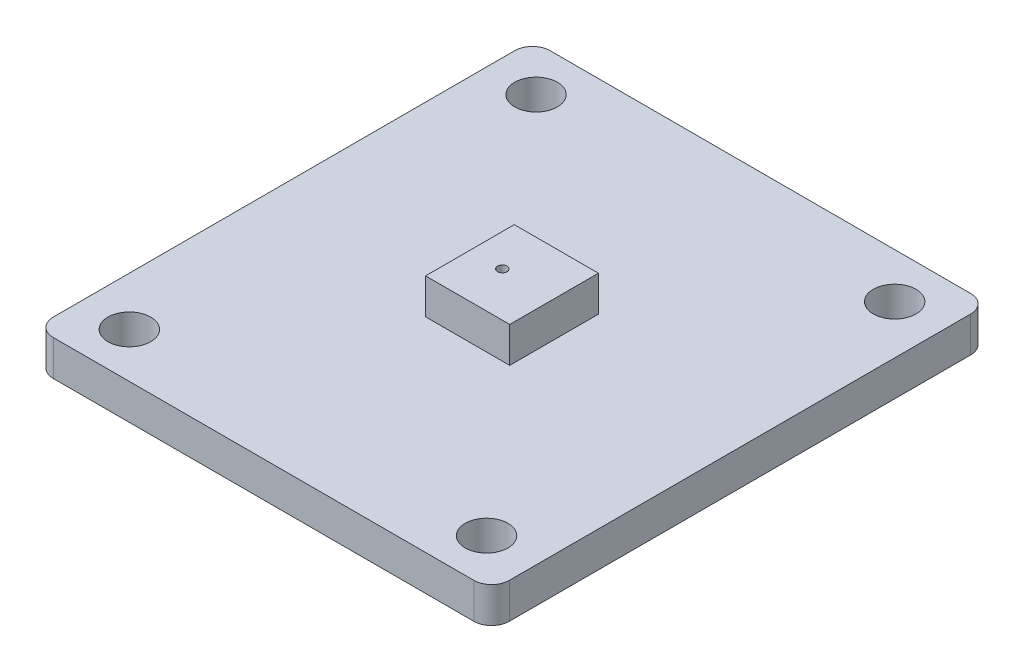
SolidWorks part; units mm, degrees
ref_plane "Front Plane" through (0, 0, 0) normal (0, 0, 1) x (1, 0, 0)
ref_plane "Top Plane" through (0, 0, 0) normal (0, 1, 0) x (1, 0, 0)
ref_plane "Right Plane" through (0, 0, 0) normal (1, 0, 0) x (0, 0, -1)
sketch "Sketch1" plane through (0, 0, 0) normal (0, 1, 0) x (1, 0, 0)
  line L0 (0, 33.0132) -> (0, -40.1974) construction
  line L1 (-39.7982, 0) -> (55.6491, 0) construction
  line L3 (-11.85, 14) -> (11.85, 14)
  line L4 (-12.85, 13) -> (-12.85, -13)
  line L5 (-11.85, -14) -> (11.85, -14)
  line L6 (12.85, 13) -> (12.85, -13)
  arc A0 (-12.85, -13) -> (-11.85, -14) centre (-11.85, -13) ccw
  arc A1 (11.85, -14) -> (12.85, -13) centre (11.85, -13) ccw
  arc A2 (11.85, 14) -> (12.85, 13) centre (11.85, 13) cw
  arc A3 (-11.85, 14) -> (-12.85, 13) centre (-11.85, 13) ccw
  circle A4 centre (-10.105, 11.46) radius 1.205
  circle A5 centre (-10.105, -11.46) radius 1.205
  circle A6 centre (10.0266, -11.46) radius 1.205
  circle A7 centre (10.105, 11.46) radius 1.205
  point P9 (0, 0)
  point P10 (0, 0)
  point P15 (-12.85, -14)
  point P18 (12.85, -14)
  point P21 (12.85, 14)
  point P24 (-12.85, 14)
  point P33 (-11.31, 11.46)
  point P34 (11.31, 11.46)
  point P35 (-10.105, 12.665)
  point P36 (-10.105, -12.665)
  dimension "D3" = 1
  dimension "D6" = 2.41
  dimension "D1" = 25.7
  dimension "D2" = 28
  dimension "D4" = 25.33
  dimension "D5" = 22.62
extrude "Boss-Extrude1" add sketch "Sketch1" along normal blind 2
sketch "Sketch2" plane through (0, 0, 0) normal (0, 1, 0) x (1, 0, 0)
  line L0 (-2.37, 2.5) -> (2.37, 2.5)
  line L1 (-2.37, 2.5) -> (-2.37, -2.5)
  line L2 (-2.37, -2.5) -> (2.37, -2.5)
  line L3 (2.37, 2.5) -> (2.37, -2.5)
  circle A0 centre (-0.5484, 0) radius 0.2718
extrude "Boss-Extrude2" add sketch "Sketch2" along normal blind 4
